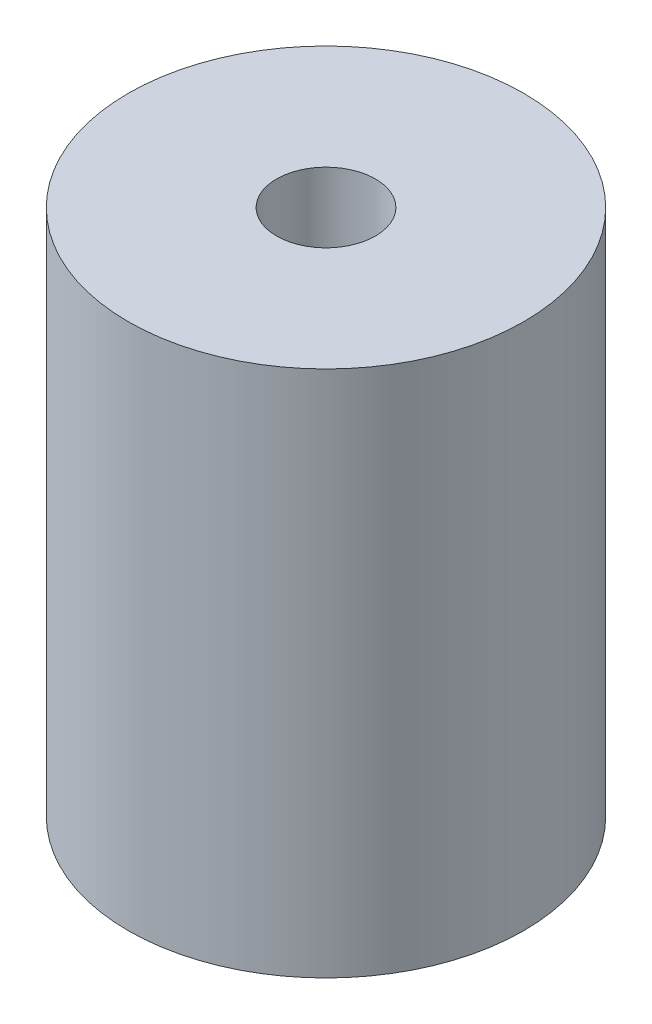
SolidWorks part; units mm, degrees
ref_plane "Front" through (0, 0, 0) normal (0, 0, 1) x (1, 0, 0)
ref_plane "Top" through (0, 0, 0) normal (0, 1, 0) x (1, 0, 0)
ref_plane "Right" through (0, 0, 0) normal (1, 0, 0) x (0, 0, -1)
sketch "Sketch1" plane through (0, 0, 0) normal (0, 1, 0) x (1, 0, 0)
  circle A0 centre (0, 0) radius 12
  circle A1 centre (0, 0) radius 3
  dimension "D1" = 24
  dimension "D2" = 6
extrude "Boss-Extrude1" add sketch "Sketch1" along normal mid plane 32
